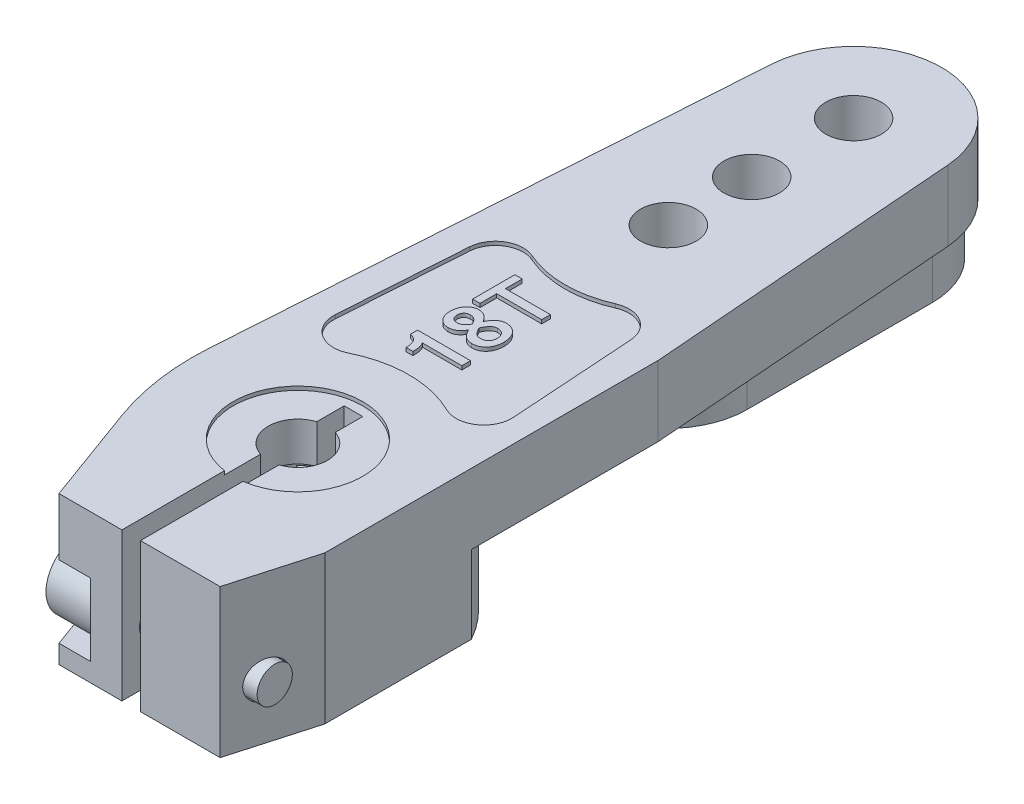
SolidWorks part; units mm, degrees
ref_plane "Plan de face" through (0, 0, 0) normal (0, 0, 1) x (1, 0, 0)
ref_plane "Plan de dessus" through (0, 0, 0) normal (0, 1, 0) x (1, 0, 0)
ref_plane "Plan de droite" through (0, 0, 0) normal (1, 0, 0) x (0, 0, -1)
sketch "Esquisse2" plane through (0, 0, 0) normal (0, 1, 0) x (1, 0, 0)
  circle A0 centre (0, 0) radius 6.75
  dimension "D1" = 13.5
extrude "Boss.-Extru.1" add sketch "Esquisse2" along normal blind 8
sketch "Esquisse3" plane through (0, 0, 0) normal (0, -1, 0) x (1, 0, 0)
  circle A0 centre (0, 0) radius 3.9
  dimension "D1" = 7.8
extrude "Enlèv. mat.-Extru.1" cut sketch "Esquisse3" against normal blind 5.7
sketch "Esquisse4" plane through (0, 0, 0) normal (0, -1, 0) x (1, 0, 0)
  line L0 (-2.4374, 3.9) -> (3.642, 3.9) construction
  line L1 (3.642, 3.9) -> (0, 0) construction
  line L2 (0, 0) -> (0, 3.9) construction
  line L5 (-0.4, 3.9) -> (0.4, 3.9)
  line L6 (-0.4, 3.9) -> (-0.15, 3.2)
  line L7 (-0.15, 3.2) -> (0.15, 3.2)
  line L8 (0.15, 3.2) -> (0.4, 3.9)
  circle A1 centre (0, 0) radius 3.9 construction
  point P6 (0.1537, 3.2)
  dimension "D1" = 0.7
  dimension "D2" = 0.8
  dimension "D3" = 0.3
extrude "Boss.-Extru.2" add sketch "Esquisse4" against normal blind 4
pattern_circular "Répétition circulaire1" count 18 over 360 about axis through (0, 0, 0) along (0, 1, 0) of "Boss.-Extru.2"
sketch "Esquisse5" plane through (0, 8, 0) normal (0, 1, 0) x (1, 0, 0)
  line L0 (-3.9, -9) -> (4.8, -9)
  line L1 (4.8, -9) -> (6.05, -4.6)
  line L2 (6.05, -4.6) -> (6.05, 13.4)
  line L3 (6.05, 13.4) -> (4.7358, 30.3668)
  line L4 (-4.7394, 30.3167) -> (-6.8301, -0.9741)
  line L5 (-6.8301, -0.9741) -> (-3.9, -9)
  line L6 (-3.9, 0) -> (-3.9, -25.8146) construction
  circle A0 centre (0, 0) radius 6.75 construction
  circle A2 centre (0, 0) radius 6.75 construction
  arc A3 (-3.8894, 0.2868) -> (-3.8894, -0.2868) centre (0, 0) ccw construction
  arc A4 (4.7358, 30.3668) -> (-4.7394, 30.3167) centre (0, 30) ccw
  circle A5 centre (0, 30) radius 1.5
  circle A6 centre (0, 24.5) radius 1.5
  circle A7 centre (0, 20) radius 1.5
  circle A8 centre (0, 0) radius 4.125
  point P19 (-6.75, 0)
  dimension "D6" = 3
  dimension "D7" = 3
  dimension "D8" = 3
  dimension "D12" = 4.75
  dimension "D13" = 8.25
  dimension "D1" = 8.7
  dimension "D2" = 4.4
  dimension "D3" = 12.8
  dimension "D4" = 9
  dimension "D5" = 18
  dimension "D9" = 20
  dimension "D10" = 24.5
  dimension "D11" = 30
extrude "Boss.-Extru.3" add sketch "Esquisse5" against normal up to surface (8 mm away) up to face at (0, 0, 0)
sketch "Esquisse6" plane through (0, 0, 0) normal (0, -1, 0) x (1, 0, 0)
  line L0 (6.05, -2.9933) -> (6.05, 2.9933)
  line L1 (6.05, 2.9933) -> (12.0451, 2.9933)
  line L2 (12.0451, 2.9933) -> (12.0451, -2.9933)
  line L3 (12.0451, -2.9933) -> (6.05, -2.9933)
extrude "Enlèv. mat.-Extru.2" cut sketch "Esquisse6" against normal blind 8
fillet "Congé1" radius 13.5 1 edges at (-6.8301, 4, 0.9741)
sketch "Esquisse7" plane through (0, 0, 0) normal (0, -1, 0) x (1, 0, 0)
  line L0 (6.05, -13.4) -> (6.05, 4.6) construction
  line L1 (-6.6398, -1.8741) -> (-4.7394, -30.3167)
  line L2 (4.7358, -30.3668) -> (6.05, -13.4)
  line L3 (6.05, -13.4) -> (6.05, -3.3162)
  line L4 (-6.6398, -1.8741) -> (-4.7394, -30.3167) construction
  arc A0 (-6.6398, -1.8741) -> (6.05, -3.3162) centre (0, 0) ccw
  arc A2 (-4.7394, -30.3167) -> (4.7358, -30.3668) centre (0, -30) ccw
  point P4 (-6.2636, -2.5158)
  point P14 (-6.6398, -1.8741)
extrude "Enlèv. mat.-Extru.5" cut sketch "Esquisse7" against normal blind 1.5
sketch "Esquisse8" plane through (0, 1.5, 0) normal (0, -1, 0) x (1, 0, 0)
  line L0 (0, -30) -> (0, -20) construction
  line L1 (-4.25, -30) -> (-4.25, -20)
  line L2 (4.25, -30) -> (4.25, -20)
  line L14 (-6.6398, -1.8741) -> (-4.7394, -30.3167)
  line L15 (4.7358, -30.3668) -> (6.05, -13.4)
  line L16 (6.05, -13.4) -> (6.05, -3.3162)
  line L17 (-6.6398, -1.8741) -> (-4.7394, -30.3167)
  line L18 (4.7358, -30.3668) -> (6.05, -13.4)
  line L19 (6.05, -13.4) -> (6.05, -3.3162)
  arc A0 (-4.25, -30) -> (4.25, -30) centre (0, -30) ccw
  arc A1 (4.25, -20) -> (-4.25, -20) centre (0, -20) ccw
  arc A12 (-6.6398, -1.8741) -> (6.05, -3.3162) centre (0, 0) ccw
  arc A13 (-4.7394, -30.3167) -> (4.7358, -30.3668) centre (0, -30) ccw
  arc A14 (-6.6398, -1.8741) -> (6.05, -3.3162) centre (0, 0) ccw
  arc A15 (-4.7394, -30.3167) -> (4.7358, -30.3668) centre (0, -30) ccw
  point P3 (0, -25)
  dimension "D2" = 0.5
  dimension "D1" = 0
extrude "Enlèv. mat.-Extru.6" cut sketch "Esquisse8" against normal blind 2.7
sketch "Esquisse9" plane through (0, 1.5, 0) normal (0, -1, 0) x (1, 0, 0)
  line L1 (-1, -6.8264) -> (1, -6.8264)
  line L2 (-1, -6.8264) -> (-1, -15.8693)
  line L3 (-1, -15.8693) -> (1, -15.8693)
  line L4 (1, -6.8264) -> (1, -15.8693)
  arc A0 (-6.6398, -1.8741) -> (6.05, -3.3162) centre (0, 0) ccw construction
  arc A1 (4.25, -20) -> (-4.25, -20) centre (0, -20) ccw construction
  dimension "D1" = 2
  dimension "D2" = 1
extrude "Boss.-Extru.4" add sketch "Esquisse9" against normal up to surface (2.7 mm away) up to face at (0, 4.2, -25)
fillet "Congé2" radius 2 4 edges at (-1, 2.85, -15.8693) (1, 2.85, -15.8693) (1, 2.85, -6.8264) (-1, 2.85, -6.8264)
sketch "Esquisse10" plane through (0, 5.7, 0) normal (0, -1, 0) x (1, 0, 0)
  circle A0 centre (0, 0) radius 1.6
  dimension "D1" = 3.2
extrude "Enlèv. mat.-Extru.7" cut sketch "Esquisse10" against normal blind 4
sketch "Esquisse11" plane through (0, 8, 0) normal (0, -1, 0) x (1, 0, 0)
  line L0 (4.8, 9) -> (-3.9, 9) construction
  line L1 (-0.5, 9) -> (0.5, 9)
  line L2 (-0.5, 9) -> (-0.5, -3)
  line L3 (-0.5, -3) -> (0.5, -3)
  line L4 (0.5, 9) -> (0.5, -3)
  dimension "D1" = 1
  dimension "D2" = 0.5
  dimension "D3" = 12
extrude "Enlèv. mat.-Extru.8" cut sketch "Esquisse11" along normal up to surface (8 mm away) up to face at (-0.044, 0, 2.8078)
sketch "Esquisse12" plane through (0, 8, 0) normal (0, 1, 0) x (1, 0, 0)
  circle A0 centre (0, 0) radius 3.5
  dimension "D1" = 7
extrude "Enlèv. mat.-Extru.9" cut sketch "Esquisse12" against normal blind 0.2
ref_plane "Plan1" through (-2.2, 0, 0) normal (1, 0, 0) x (0, 0, -1)
sketch "Esquisse13" plane through (-2.2, 0, 0) normal (1, 0, 0) x (0, 0, -1)
  line L0 (-9, 4.9) -> (-7.05, 4.9)
  line L1 (-9, 0) -> (-9, 8) construction
  line L2 (-7.05, 1) -> (-9, 1)
  line L3 (-9, 1) -> (-9, 4.9)
  line L4 (-9, 0) -> (-3.6556, 0) construction
  arc A0 (-7.05, 4.9) -> (-7.05, 1) centre (-7.05, 2.95) cw
  point P9 (-5.1, 2.95)
  dimension "D1" = 3.9
  dimension "D2" = 1
  dimension "D3" = 3.9
extrude "Enlèv. mat.-Extru.10" cut sketch "Esquisse13" against normal blind 5
sketch "Esquisse14" plane through (-2.2, 0, 0) normal (-1, 0, 0) x (0, 0, 1)
  circle A0 centre (7.05, 2.95) radius 1
  dimension "D1" = 2
extrude "Enlèv. mat.-Extru.11" cut sketch "Esquisse14" against normal blind 9
sketch "Esquisse15" plane through (0, 8, 0) normal (0, 1, 0) x (1, 0, 0)
  line L0 (-4.8053, 6.8307) -> (-4.3517, 13.6201)
  line L2 (4.3517, 13.6201) -> (4.8053, 6.8307)
  line L4 (-4.7394, 30.3167) -> (-6.6398, 1.8741) construction
  line L5 (0, 16) -> (0, -2.0295) construction
  arc A0 (2.6469, 5.3846) -> (4.8053, 6.8307) centre (3.3086, 6.7307) ccw
  arc A1 (-2.6469, 5.3846) -> (2.6469, 5.3846) centre (0, 0) cw
  arc A2 (-2.2502, 14.8927) -> (2.2502, 14.8927) centre (0, 20) ccw
  arc A3 (2.2502, 14.8927) -> (4.3517, 13.6201) centre (2.855, 13.5201) cw
  arc A4 (-4.3517, 13.6201) -> (-2.2502, 14.8927) centre (-2.855, 13.5201) cw
  arc A5 (-4.8053, 6.8307) -> (-2.6469, 5.3846) centre (-3.3086, 6.7307) ccw
  point P3 (0, 0)
  point P15 (0, 0)
  dimension "D2" = 5.581
  dimension "D1" = 6
  dimension "D4" = 1.5
  dimension "D3" = 1.5
extrude "Enlèv. mat.-Extru.12" cut sketch "Esquisse15" against normal blind 0.2
sketch "Esquisse16" plane through (0, 7.8, 0) normal (0, 1, 0) x (1, 0, 0)
  line L0 (1, 6.765) -> (1, 13.1716) construction
  text T0 "18T" font "Microsoft Sans Serif" height in points 11
  point P3 (2, 6.765)
  dimension "D1" = 1
extrude "Boss.-Extru.5" add sketch "Esquisse16" along normal blind 0.2
sketch "Esquisse17" plane through (-2.2, 0, 0) normal (-1, 0, 0) x (0, 0, 1)
  circle A0 centre (7.05, 2.95) radius 1.85
  dimension "D1" = 3.7
extrude "Boss.-Extru.6" add sketch "Esquisse17" along normal blind 2.5
sketch "Esquisse18" plane through (-4.7, 0, 0) normal (-1, 0, 0) x (0, 0, 1)
  line L1 (7.6274, 1.95) -> (8.2047, 2.95)
  line L2 (8.2047, 2.95) -> (7.6274, 3.95)
  line L3 (7.6274, 3.95) -> (6.4726, 3.95)
  line L4 (6.4726, 3.95) -> (5.8953, 2.95)
  line L5 (5.8953, 2.95) -> (6.4726, 1.95)
  line L6 (6.4726, 1.95) -> (7.6274, 1.95)
  circle A0 centre (7.05, 2.95) radius 1 construction
  dimension "D1" = 2
extrude "Enlèv. mat.-Extru.13" cut sketch "Esquisse18" against normal blind 1.5
sketch "Esquisse19" plane through (-2.2, 0, 0) normal (1, 0, 0) x (0, 0, -1)
  circle A0 centre (-7.05, 2.95) radius 0.95
  dimension "D1" = 1.9
extrude "Boss.-Extru.7" add sketch "Esquisse19" along normal blind 8
